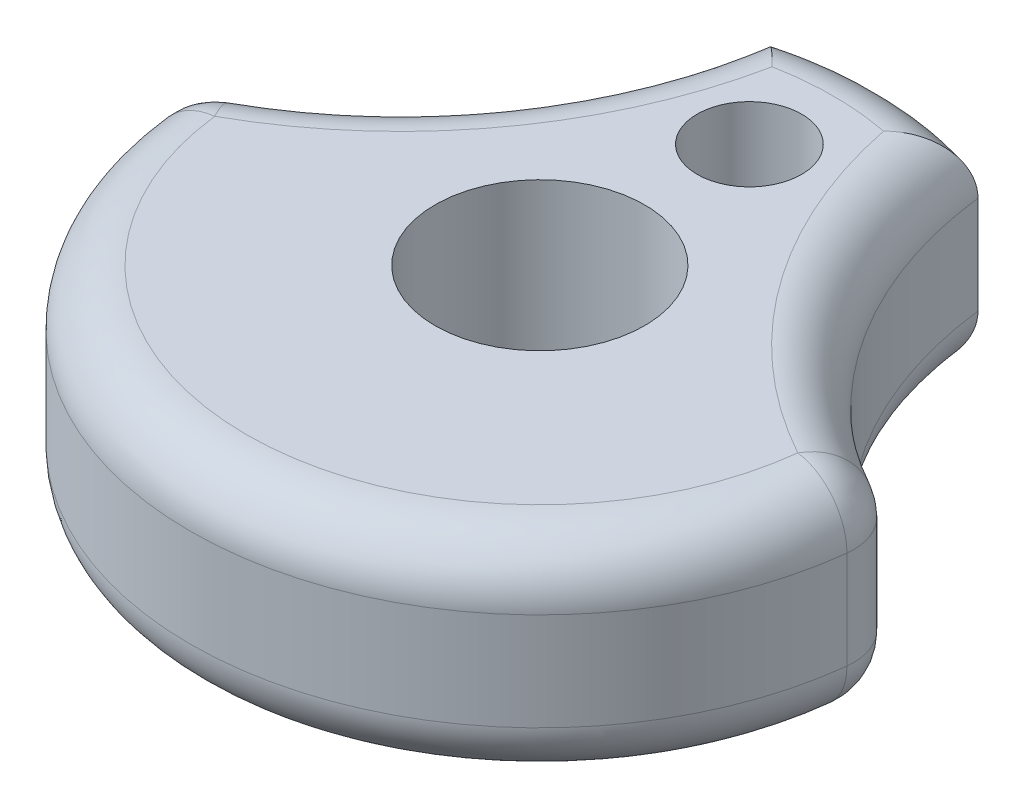
SolidWorks part; units mm, degrees
material "Plain Carbon Steel"
ref_plane "Front Plane" through (0, 0, 0) normal (0, 0, 1) x (1, 0, 0)
ref_plane "Top Plane" through (0, 0, 0) normal (0, 1, 0) x (1, 0, 0)
ref_plane "Right Plane" through (0, 0, 0) normal (1, 0, 0) x (0, 0, -1)
sketch "Sketch1" plane through (0, 0, 0) normal (0, 1, 0) x (1, 0, 0)
  line L0 (0, 72.2139) -> (0, -7.9096) construction
  line L1 (0, -55) -> (0, 55) construction
  arc A2 (-4.7752, 15.1398) -> (-15.875, 0) centre (-23.694, 17.3714) cw
  arc A3 (4.7752, 15.1398) -> (15.875, 0) centre (23.694, 17.3714) ccw
  arc A4 (-15.875, 0) -> (15.875, 0) centre (0, 0) ccw
  arc A5 (-4.7752, 15.1398) -> (4.7752, 15.1398) centre (0, 0) cw
  dimension "D2" = 4.7752
extrude "Boss-Extrude1" add sketch "Sketch1" along normal blind 9.525
sketch "Sketch2" plane through (0, 9.525, 0) normal (0, 1, 0) x (1, 0, 0)
  line L0 (0, -5.2388) -> (0, 5.2388) construction
  circle A0 centre (0, 0) radius 4.7625
  circle A1 centre (0, 9.525) radius 2.3749
  dimension "D1" = 9.525
  dimension "D3" = 4.7498
  dimension "D2" = 9.525
extrude "Cut-Extrude1" cut sketch "Sketch2" against normal through all
fillet "Fillet4" radius 2.54 10 edges at (-15.875, 4.7625, 0) (0, 9.525, 15.875) (0, 0, 15.875) (15.875, 4.7625, 0) (8.3307, 0, -6.1077) (8.3307, 9.525, -6.1077) (-8.3307, 9.525, -6.1077) (-8.3307, 0, -6.1077) (0, 0, -15.875) (0, 9.525, -15.875)
